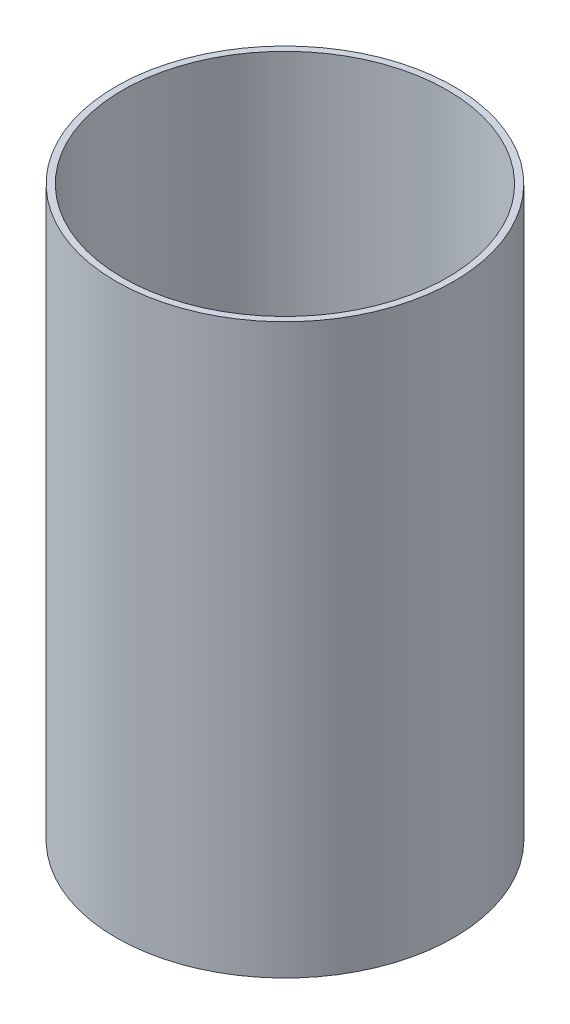
SolidWorks part; units mm, degrees
material "PTFE (general)"
ref_plane "Front Plane" through (0, 0, 0) normal (0, 0, 1) x (1, 0, 0)
ref_plane "Top Plane" through (0, 0, 0) normal (0, 1, 0) x (1, 0, 0)
ref_plane "Right Plane" through (0, 0, 0) normal (1, 0, 0) x (0, 0, -1)
ref_axis "Axis1" through (0, 55, 0) along (0, -1, 0)
sketch "Sketch2" plane through (0, 0, 0) normal (0, 0, 1) x (1, 0, 0)
  line L1 (-39.624, 0) -> (-38.1, 0)
  line L2 (-39.624, 0) -> (-39.624, -133.35)
  line L3 (-39.624, -133.35) -> (-38.1, -133.35)
  line L4 (-38.1, 0) -> (-38.1, -133.35)
  dimension "D2" = 1.524
revolve "Revolve1" add sketch "Sketch2" angle 360 about axis through (0, 55, 0) along (0, -1, 0)
equation "\"D2@Sketch2\"=\"LINER THICKNESS@Cryo Tank.SLDASM\""
